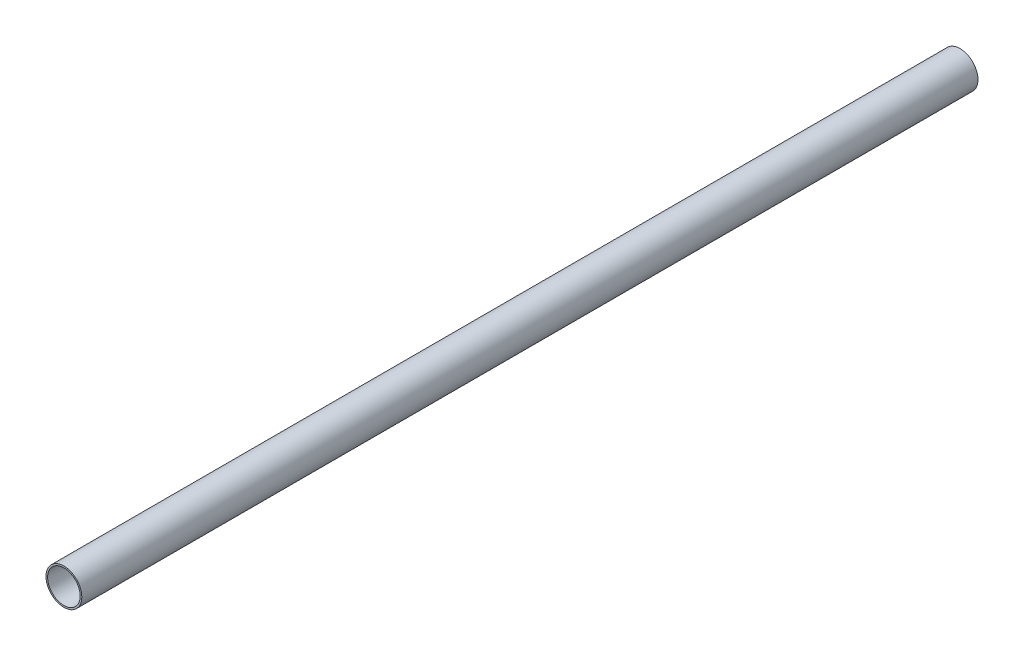
SolidWorks part; units mm, degrees
material "Carbon Fiber Tube - UD Approx"
ref_plane "Front Plane" through (0, 0, 0) normal (0, 0, 1) x (1, 0, 0)
ref_plane "Top Plane" through (0, 0, 0) normal (0, 1, 0) x (1, 0, 0)
ref_plane "Right Plane" through (0, 0, 0) normal (1, 0, 0) x (0, 0, -1)
sketch "Sketch1" plane through (0, 0, 0) normal (0, 0, 1) x (1, 0, 0)
  circle A0 centre (0, 0) radius 11
  circle A1 centre (0, 0) radius 10
  dimension "D1" = 22
  dimension "D2" = 20
extrude "Boss-Extrude1" add sketch "Sketch1" along normal blind 550
